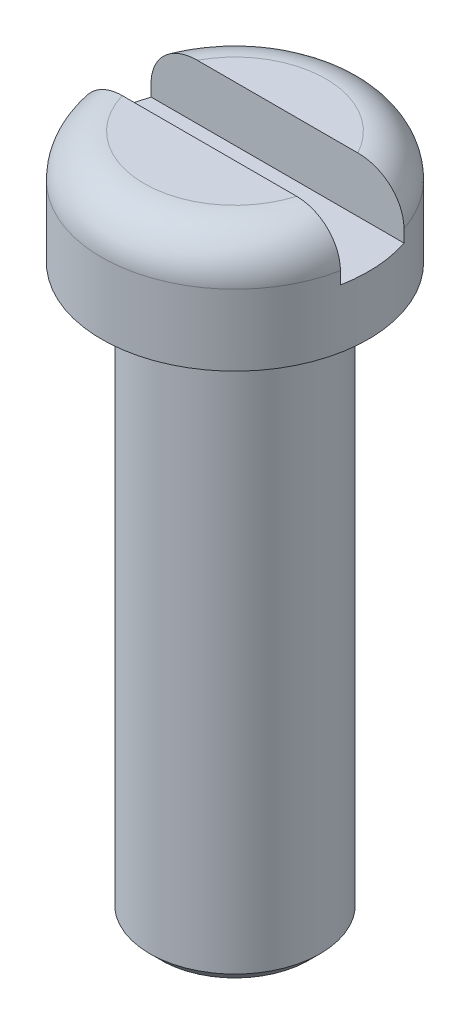
SolidWorks part; units mm, degrees
material "Plain Carbon Steel"
ref_plane "Front Plane" through (0, 0, 0) normal (0, 0, 1) x (1, 0, 0)
ref_plane "Top Plane" through (0, 0, 0) normal (0, 1, 0) x (1, 0, 0)
ref_plane "Right Plane" through (0, 0, 0) normal (1, 0, 0) x (0, 0, -1)
ref_plane "Plane1" through (0, 0, 0) normal (1, 0, 0) x (0, 0, -1)
sketch "Sketch1" plane through (0, 0, 0) normal (1, 0, 0) x (0, 0, -1)
  line L0 (1.5, -10) -> (0, -10)
  line L1 (1.5, 0) -> (1.5, -10)
  line L2 (1.5, 0) -> (2.35, 0)
  line L3 (2.35, 0) -> (2.35, 1.25)
  line L4 (1.6, 2) -> (0, 2)
  line L5 (0, 2) -> (0, -10)
  line L6 (0, -26.35) -> (0, 3.35) construction
  arc A0 (2.35, 1.25) -> (1.6, 2) centre (1.6, 1.25) ccw
  dimension "D1" = 10
  dimension "D2" = 1.6
  dimension "D3" = 1.25
revolve "Revolve1" add sketch "Sketch1" angle 360 about L6
ref_plane "Plane2" through (0, 0, 0) normal (1, 0, 0) x (0, 0, -1)
sketch "Sketch2" plane through (0, 0, 0) normal (1, 0, 0) x (0, 0, -1)
  line L0 (-0.45, 4) -> (0.75, 4)
  line L1 (0.75, 4) -> (0.75, 1.0317)
  line L2 (0.75, 1.0317) -> (-0.45, 1.0317)
  line L3 (-0.45, 1.0317) -> (-0.45, 4)
extrude "Cut-Extrude1" cut sketch "Sketch2" against normal through all and the other way through all
chamfer "Фаска1" distance 0.2 angle 45 1 edges at (0, -10, -1.5)
